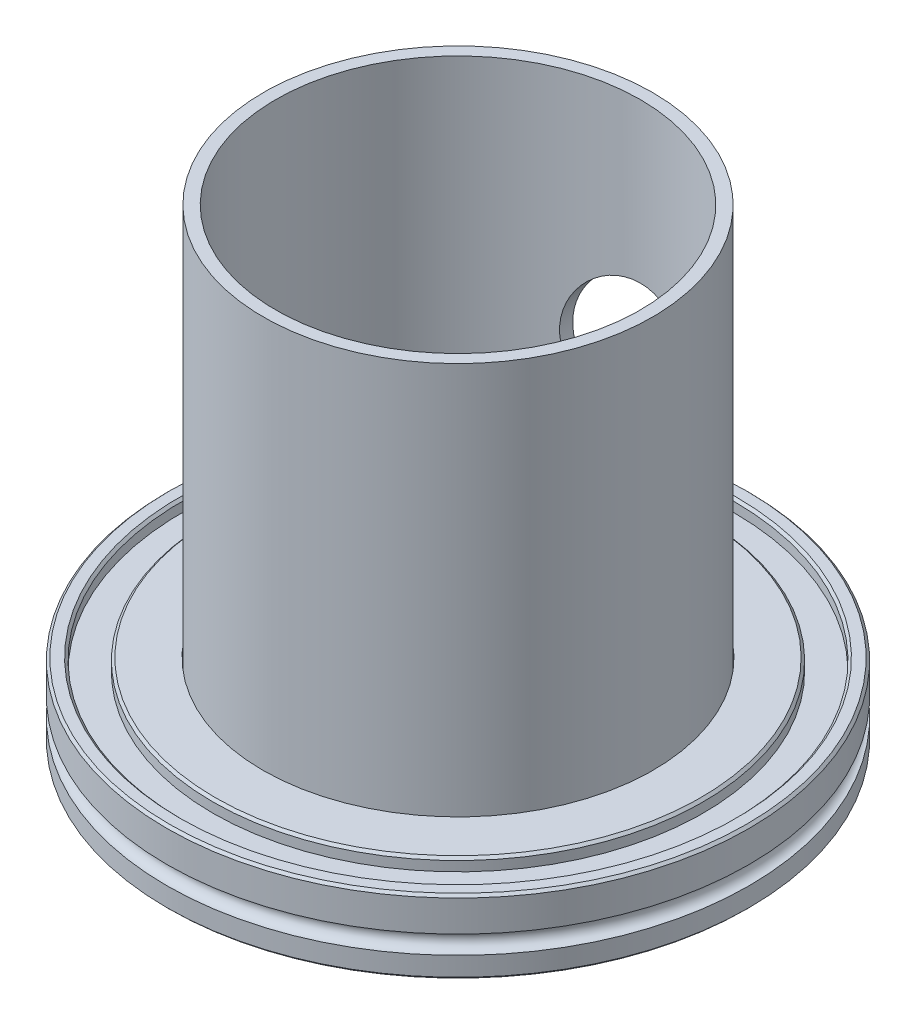
SolidWorks part; units mm, degrees
ref_plane "Front Plane" through (0, 0, 0) normal (0, 0, 1) x (1, 0, 0)
ref_plane "Top Plane" through (0, 0, 0) normal (0, 1, 0) x (1, 0, 0)
ref_plane "Right Plane" through (0, 0, 0) normal (1, 0, 0) x (0, 0, -1)
ref_plane "Plane1" through (0, 0, 0) normal (0, 0, -1) x (-1, 0, 0)
sketch "Sketch5" plane through (0, 0, 0) normal (0, 0, -1) x (-1, 0, 0)
  line L0 (-47.1, 12) -> (-47.5, 11.6)
  line L1 (-47.5, 11.6) -> (-47.5, 6.5)
  line L2 (-47.5, 3.5) -> (-47.5, 0.4)
  line L3 (-47.5, 0.4) -> (-47.1, 0)
  line L4 (-47.1, 0) -> (-35.4, 0)
  line L5 (-35.4, 0) -> (-35, 0.4)
  line L6 (-35, 0.4) -> (-35, 4.5)
  line L7 (-35, 4.5) -> (-30.15, 4.5)
  line L8 (-30.15, 4.5) -> (-30.15, 6.5)
  line L9 (-30.15, 6.5) -> (-31.85, 6.5)
  line L10 (-31.85, 6.5) -> (-31.85, 12)
  line L11 (-31.85, 12) -> (-39.6, 12)
  line L12 (-39.6, 12) -> (-40, 11.6)
  line L13 (-40, 11.6) -> (-40, 10)
  line L14 (-40, 10) -> (-45, 10)
  line L15 (-45, 10) -> (-45, 11.6)
  line L16 (-45, 11.6) -> (-45.4, 12)
  line L17 (-45.4, 12) -> (-47.1, 12)
  line L18 (0, 0) -> (0, 12) construction
  arc A0 (-47.5, 6.5) -> (-47.5, 3.5) centre (-47.5, 5) cw
revolve "ISO-63K" add sketch "Sketch5" angle 360 about L18
sketch "Sketch7" plane through (0, 0, 0) normal (0, 0, 1) x (1, 0, 0)
  line L0 (31.75, 76) -> (29.75, 76)
  line L1 (29.75, 76) -> (29.75, 6.5)
  line L2 (29.75, 6.5) -> (31.75, 6.5)
  line L3 (31.75, 6.5) -> (31.75, 76)
  line L4 (0, 88) -> (0, 6.5) construction
revolve "Half-Nipple" add sketch "Sketch7" angle 360 about L4
sketch "Sketch9" plane through (0, 0, 0) normal (0, 0, 1) x (1, 0, 0)
  line L0 (31.85, 12) -> (-31.85, 12) construction
  circle A0 centre (0, 39) radius 11.05
  dimension "D2" = 22.1
  dimension "D1" = 27
extrude "Cut-Extrude1" cut sketch "Sketch9" against normal through all
sketch "Sketch10" plane through (0, 0, 0) normal (0, 0, 1) x (1, 0, 0)
  circle A0 centre (0, 39) radius 11.05
